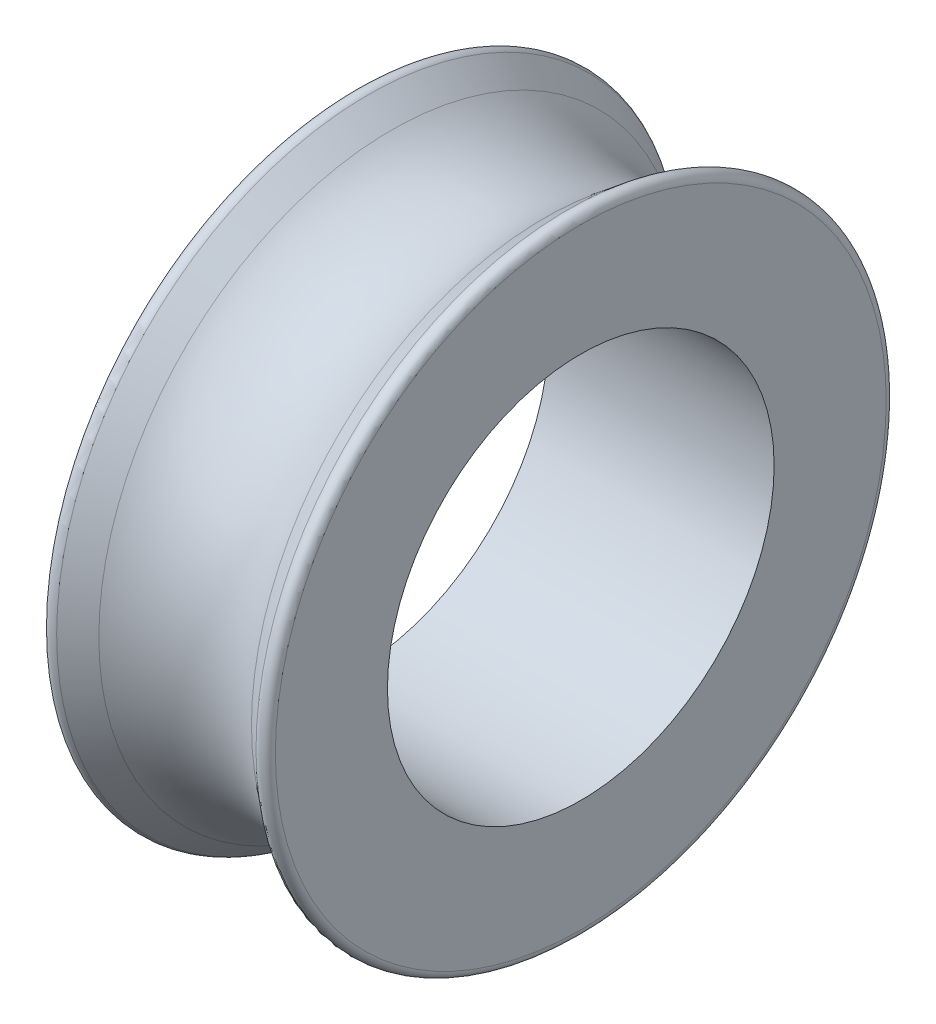
SolidWorks part; units mm, degrees
ref_plane "Front Plane" through (0, 0, 0) normal (0, 0, 1) x (1, 0, 0)
ref_plane "Top Plane" through (0, 0, 0) normal (0, 1, 0) x (1, 0, 0)
ref_plane "Right Plane" through (0, 0, 0) normal (1, 0, 0) x (0, 0, -1)
sketch "Sketch2" plane through (0, 0, 0) normal (0, 0, 1) x (1, 0, 0)
  line L0 (0, 0) -> (7, 0)
  line L1 (7, 0) -> (7, 10)
  line L4 (0, 10) -> (0, 0)
  line L5 (0, 10) -> (1.1318, 9.0876)
  line L7 (5.8682, 9.0876) -> (7, 10)
  arc A0 (1.1318, 9.0876) -> (5.8682, 9.0876) centre (3.5, 12.0253) ccw
  point P3 (6.4834, 11.1553)
  point P9 (0.7981, 10.6177)
  dimension "D1" = 7
  dimension "D2" = 10
revolve "Revolve1" add sketch "Sketch2" angle 360 about L0
fillet "Fillet1" radius 0.25 2 edges at (7, 0, 10) (0, 0, 10)
sketch "Sketch3" plane through (0, 0, 0) normal (-1, 0, 0) x (0, 0, 1)
  circle A0 centre (0, 0) radius 6
  dimension "D1" = 12
extrude "Cut-Extrude1" cut sketch "Sketch3" against normal up to next
